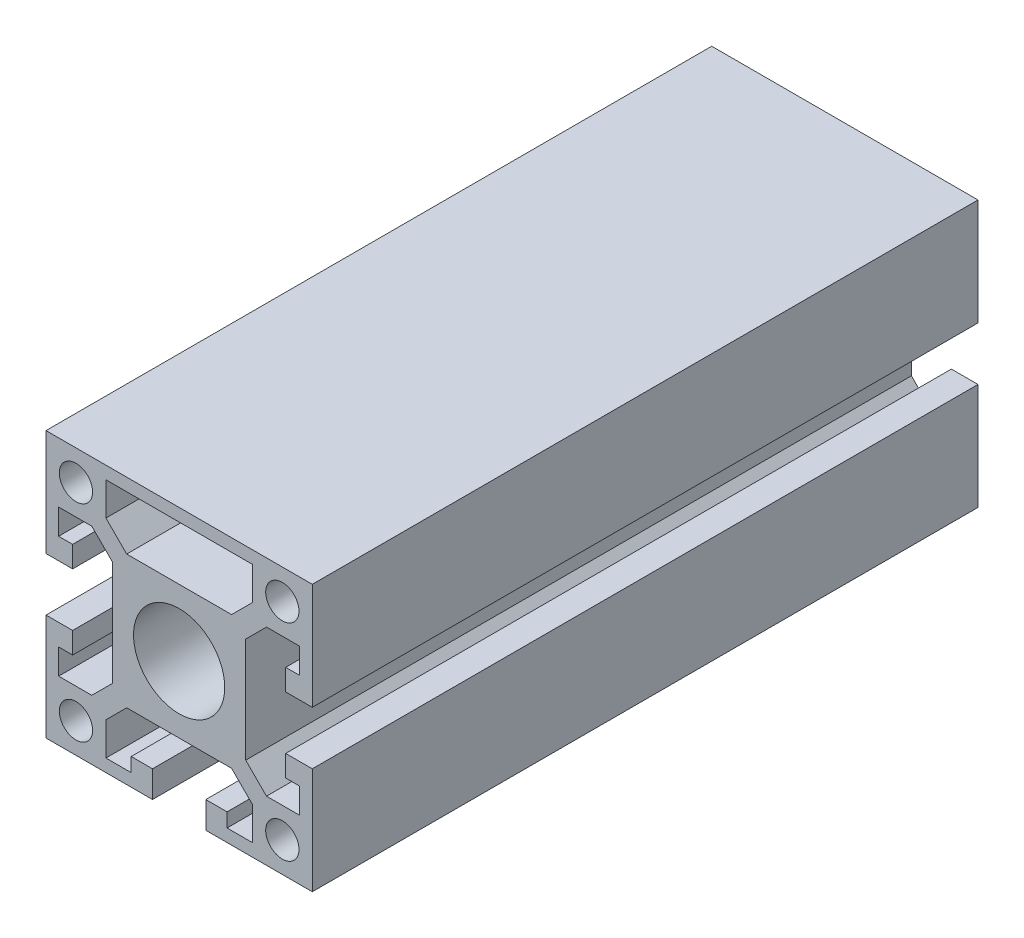
SolidWorks part; units mm, degrees
ref_plane "Front" through (0, 0, 0) normal (0, 0, 1) x (1, 0, 0)
ref_plane "Top" through (0, 0, 0) normal (0, 1, 0) x (1, 0, 0)
ref_plane "Right" through (0, 0, 0) normal (1, 0, 0) x (0, 0, -1)
sketch "C02-1" plane through (0, 0, 0) normal (0, 0, 1) x (1, 0, 0)
  line L0 (-4, 20) -> (4, 20)
  line L1 (-4, 18.1) -> (4, 18.1)
  line L60 (-20, -4) -> (-16, -4)
  line L61 (-16, -4) -> (-16, -7.2)
  line L62 (-16, -7.2) -> (-18.1, -7.2)
  line L63 (-18.1, -7.2) -> (-18.1, -11)
  line L64 (-18.1, -11) -> (-13.1213, -11)
  line L65 (-13.1213, -11) -> (-10, -7.8787)
  line L66 (-10, -7.8787) -> (-10, 7.8787)
  line L67 (-10, 7.8787) -> (-13.1213, 11)
  line L68 (-13.1213, 11) -> (-18.1, 11)
  line L69 (-18.1, 11) -> (-18.1, 7.2)
  line L70 (-18.1, 7.2) -> (-16, 7.2)
  line L71 (-16, 7.2) -> (-16, 4)
  line L72 (-16, 4) -> (-20, 4)
  line L73 (-20, 4) -> (-20, 20)
  line L74 (-20, 20) -> (-4, 20)
  line L78 (-4, 18.1) -> (-11, 18.1)
  line L79 (-11, 18.1) -> (-11, 13.1213)
  line L80 (-11, 13.1213) -> (-7.8787, 10)
  line L81 (-7.8787, 10) -> (7.8787, 10)
  line L82 (7.8787, 10) -> (11, 13.1213)
  line L83 (11, 13.1213) -> (11, 18.1)
  line L84 (11, 18.1) -> (4, 18.1)
  line L88 (4, 20) -> (20, 20)
  line L89 (20, 20) -> (20, 4)
  line L90 (20, 4) -> (16, 4)
  line L91 (16, 4) -> (16, 7.2)
  line L92 (16, 7.2) -> (18.1, 7.2)
  line L93 (18.1, 7.2) -> (18.1, 11)
  line L94 (18.1, 11) -> (13.1213, 11)
  line L95 (13.1213, 11) -> (10, 7.8787)
  line L96 (10, 7.8787) -> (10, -7.8787)
  line L97 (10, -7.8787) -> (13.1213, -11)
  line L98 (13.1213, -11) -> (18.1, -11)
  line L99 (18.1, -11) -> (18.1, -7.2)
  line L100 (18.1, -7.2) -> (16, -7.2)
  line L101 (16, -7.2) -> (16, -4)
  line L102 (16, -4) -> (20, -4)
  line L103 (20, -4) -> (20, -20)
  line L104 (20, -20) -> (4, -20)
  line L105 (4, -20) -> (4, -16)
  line L106 (4, -16) -> (7.2, -16)
  line L107 (7.2, -16) -> (7.2, -18.1)
  line L108 (7.2, -18.1) -> (11, -18.1)
  line L109 (11, -18.1) -> (11, -13.1213)
  line L110 (11, -13.1213) -> (7.8787, -10)
  line L111 (7.8787, -10) -> (-7.8787, -10)
  line L112 (-7.8787, -10) -> (-11, -13.1213)
  line L113 (-11, -13.1213) -> (-11, -18.1)
  line L114 (-11, -18.1) -> (-7.2, -18.1)
  line L115 (-7.2, -18.1) -> (-7.2, -16)
  line L116 (-7.2, -16) -> (-4, -16)
  line L117 (-4, -16) -> (-4, -20)
  line L118 (-4, -20) -> (-20, -20)
  line L119 (-20, -20) -> (-20, -4)
  circle A5 centre (-15.5, -15.5) radius 2.5
  circle A6 centre (-15.5, 15.5) radius 2.5
  circle A7 centre (15.5, -15.5) radius 2.5
  circle A8 centre (15.5, 15.5) radius 2.5
  circle A9 centre (0, 0) radius 6.85
extrude "Extrude1" add sketch "C02-1" against normal blind 100
